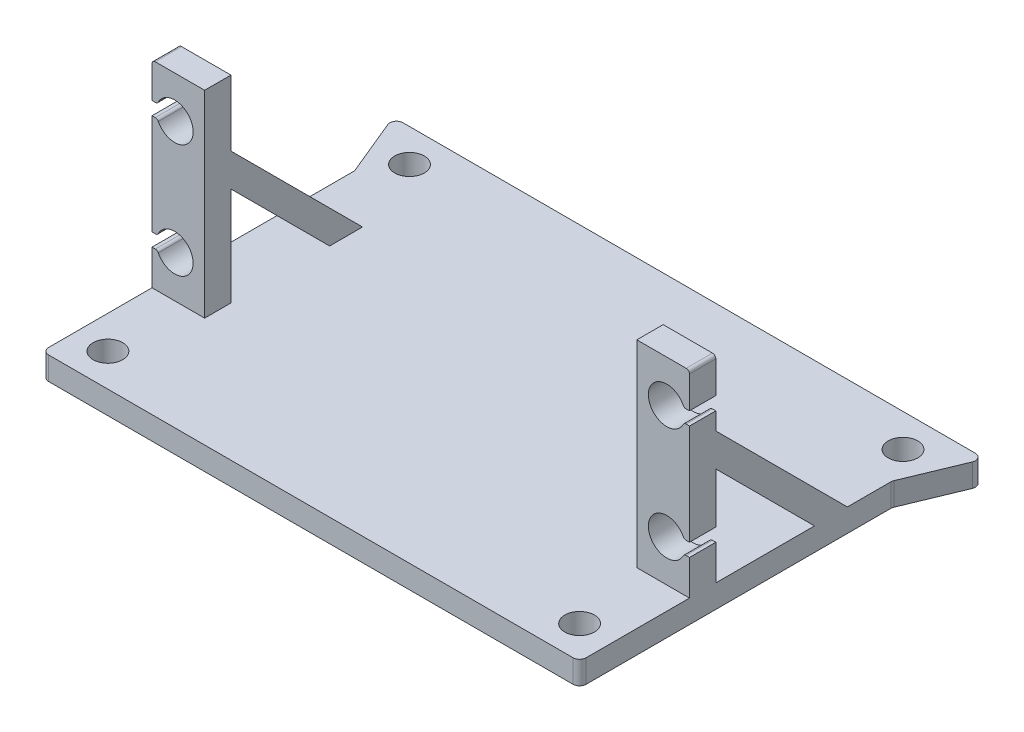
SolidWorks part; units mm, degrees
ref_plane "Front Plane" through (0, 0, 0) normal (0, 0, 1) x (1, 0, 0)
ref_plane "Top Plane" through (0, 0, 0) normal (0, 1, 0) x (1, 0, 0)
ref_plane "Right Plane" through (0, 0, 0) normal (1, 0, 0) x (0, 0, -1)
sketch "Sketch1" plane through (0, 0, 0) normal (0, 1, 0) x (1, 0, 0)
  line L0 (40.85, 57.5) -> (40.85, 0) construction
  line L1 (0, 0) -> (81.7, 0)
  line L3 (0, 57.5) -> (81.7, 57.5)
  line L5 (0, 28.75) -> (81.7, 28.75) construction
  line L6 (0, 47.5) -> (-4.1421, 57.5)
  line L8 (-4.1421, 57.5) -> (0, 57.5)
  line L9 (0, 0) -> (0, 47.5)
  line L10 (0, 57.5) -> (0, 47.5) construction
  line L11 (85.8421, 57.5) -> (81.7, 57.5)
  line L12 (81.7, 0) -> (81.7, 47.5)
  line L13 (81.7, 57.5) -> (81.7, 47.5) construction
  line L14 (81.7, 47.5) -> (85.8421, 57.5)
  circle A0 centre (5, 5) radius 2.25
  circle A2 centre (76.7, 5) radius 2.25
  circle A7 centre (3.3409, 52.5) radius 2.25
  circle A8 centre (78.3591, 52.5) radius 2.25
  point P10 (40.85, 28.75)
  point P16 (3.3409, 52.5)
  point P23 (0, 0)
  point P24 (0, 0)
  dimension "D3" = 4.5
  dimension "D4" = 5
  dimension "D5" = 5
  dimension "D6" = 22.5
  dimension "D7" = 5
  dimension "D8" = 10
  dimension "D9" = 5
  dimension "D1" = 81.7
  dimension "D2" = 57.5
extrude "Boss-Extrude1" add sketch "Sketch1" along normal blind 3.5
sketch "Sketch2" plane through (0, 3.5, 0) normal (0, 1, 0) x (1, 0, 0)
  line L0 (0, 16.7) -> (0, 20.7)
  line L2 (0, 16.7) -> (8, 16.7)
  line L3 (40.85, 57.5) -> (40.85, 0) construction
  line L4 (85.8421, 57.5) -> (-4.1421, 57.5) construction
  line L5 (0, 0) -> (81.7, 0) construction
  line L6 (0, 20.7) -> (8, 20.7)
  line L7 (8, 20.7) -> (8, 16.7)
  line L8 (81.7, 20.7) -> (73.7, 20.7)
  line L9 (81.7, 16.7) -> (81.7, 20.7)
  line L10 (81.7, 16.7) -> (73.7, 16.7)
  line L11 (73.7, 20.7) -> (73.7, 16.7)
  line L12 (0, 47.5) -> (0, 0) construction
  dimension "D1" = 40.8
  dimension "D2" = 4
  dimension "D3" = 8
extrude "Boss-Extrude2" add sketch "Sketch2" along normal blind 30
sketch "Sketch3" plane through (0, 0, -16.7) normal (0, 0, 1) x (1, 0, 0)
  line L0 (3.45, 27.15) -> (0, 27.15) construction
  line L1 (0, 33.5) -> (0, 3.5) construction
  line L2 (0.8347, 28.15) -> (0, 28.15)
  line L3 (0, 18.5) -> (81.7, 18.5) construction
  line L4 (81.7, 33.5) -> (81.7, 3.5) construction
  line L5 (40.85, 33.5) -> (40.85, 3.5) construction
  line L6 (0, 3.5) -> (81.7, 3.5) construction
  line L7 (0, 28.15) -> (0, 26.15)
  line L8 (0, 26.15) -> (0.8347, 26.15)
  line L9 (0, 10.85) -> (0.8347, 10.85)
  line L10 (0, 8.85) -> (0, 10.85)
  line L11 (0.8347, 8.85) -> (0, 8.85)
  line L12 (81.7, 8.85) -> (81.7, 10.85)
  line L13 (80.8653, 8.85) -> (81.7, 8.85)
  line L14 (81.7, 10.85) -> (80.8653, 10.85)
  line L15 (81.7, 26.15) -> (80.8653, 26.15)
  line L16 (81.7, 28.15) -> (81.7, 26.15)
  line L17 (80.8653, 28.15) -> (81.7, 28.15)
  arc A0 (0.8347, 26.15) -> (0.8347, 28.15) centre (3.45, 27.15) ccw
  arc A4 (0.8347, 10.85) -> (0.8347, 8.85) centre (3.45, 9.85) cw
  arc A5 (80.8653, 10.85) -> (80.8653, 8.85) centre (78.25, 9.85) ccw
  arc A6 (80.8653, 26.15) -> (80.8653, 28.15) centre (78.25, 27.15) cw
  point P15 (40.85, 18.5)
  dimension "D1" = 5.6
  dimension "D2" = 17.3
  dimension "D3" = 74.8
  dimension "D4" = 2
extrude "Cut-Extrude1" cut sketch "Sketch3" against normal through all
sketch "Sketch4" plane through (0, 0, 0) normal (1, 0, 0) x (0, 0, -1)
  line L0 (20.7, 23.5) -> (40.7, 3.5)
  line L1 (20.7, 3.5) -> (47.5, 3.5) construction
  line L3 (20.7, 23.5) -> (20.7, 18.5)
  line L4 (20.7, 18.5) -> (35.7, 3.5)
  line L5 (35.7, 3.5) -> (40.7, 3.5)
  line L6 (20.7, 26.15) -> (20.7, 10.85) construction
  point P4 (0, 0)
  dimension "D1" = 5
  dimension "D2" = 135
  dimension "D3" = 15
extrude "Boss-Extrude3" add sketch "Sketch4" along normal blind 8
ref_plane "Plane7" through (40.85, 0, 0) normal (1, 0, 0) x (0, 0, -1)
mirror "Mirror1" about plane through (40.85, 0, 0) normal (1, 0, 0) of "Boss-Extrude3"
fillet "Fillet3" radius 0.5 10 edges at (80.8653, 26.15, -18.7) (80.8653, 28.15, -18.7) (0.8347, 10.85, -18.7) (0.8347, 8.85, -18.7) (0, 33.5, -18.7) (81.7, 33.5, -18.7) (0.8347, 28.15, -18.7) (0.8347, 26.15, -18.7) (80.8653, 8.85, -18.7) (80.8653, 10.85, -18.7)
fillet "Fillet4" radius 1 6 edges at (0, 1.75, -47.5) (-4.1421, 1.75, -57.5) (85.8421, 1.75, -57.5) (81.7, 1.75, -47.5) (81.7, 1.75, 0) (0, 1.75, 0)
